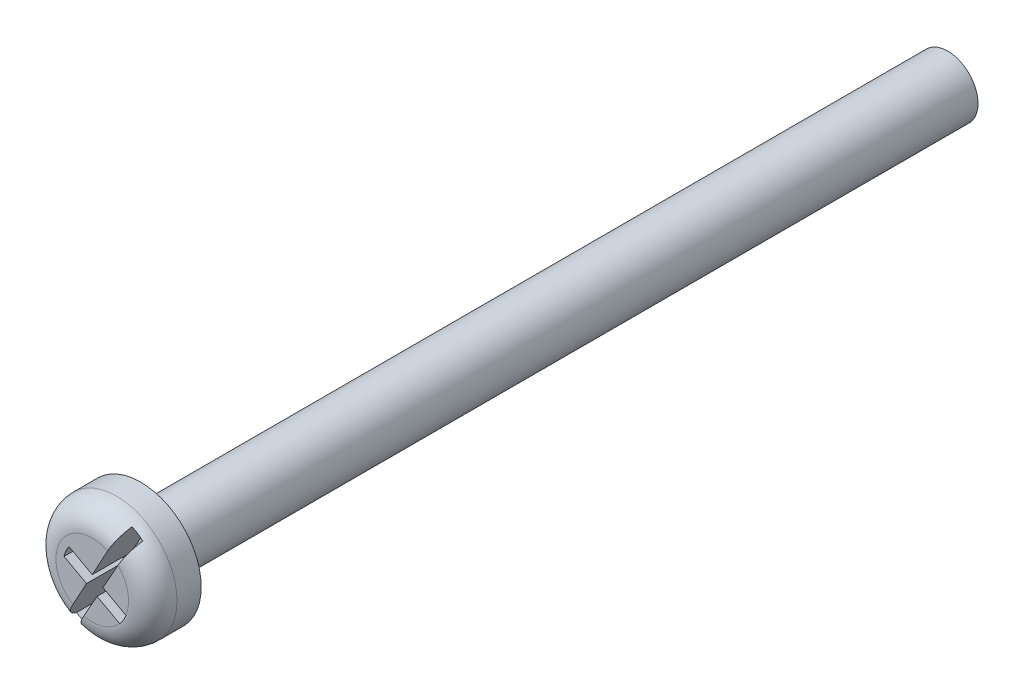
SolidWorks part; units mm, degrees
material "Stop odlewniczy stali"
ref_plane "Płaszczyzna przednia" through (0, 0, 0) normal (0, 0, 1) x (1, 0, 0)
ref_plane "Płaszczyzna górna" through (0, 0, 0) normal (0, 1, 0) x (1, 0, 0)
ref_plane "Płaszczyzna prawa" through (0, 0, 0) normal (1, 0, 0) x (0, 0, -1)
sketch "Szkic1" plane through (0, 0, 0) normal (0, 0, 1) x (1, 0, 0)
  circle A0 centre (-1.8605, 2.7321) radius 3
  dimension "D1" = 6
extrude "Dodanie-wyciągnięcie2" add sketch "Szkic1" along normal blind 2.4
sketch "Szkic2" plane through (0, 0, 0) normal (0, 0, -1) x (-1, 0, 0)
  circle A0 centre (1.8605, 2.7321) radius 1.5
extrude "Dodanie-wyciągnięcie3" add sketch "Szkic2" along normal blind 40
fillet "Zaokrąglenie2" radius 1.2 1 edges at (1.1395, 2.7321, 2.4)
sketch "Szkic3" plane through (0, 0, 2.4) normal (0, 0, 1) x (1, 0, 0)
  line L0 (-1.8595, 2.9591) -> (-0.5756, 5.3165)
  line L1 (-1.8595, 2.9591) -> (-3.0095, 3.5874)
  line L2 (-3.3345, 0.2508) -> (-2.1451, 2.4347)
  line L3 (-2.8199, 0.0102) -> (-1.6213, 2.1486)
  line L4 (-0.184, 2.0436) -> (-1.3294, 2.6694)
  line L5 (-0.4992, 1.5357) -> (-1.6213, 2.1486)
  line L6 (-1.3294, 2.6694) -> (-0.0393, 4.9711)
  line L7 (-2.1451, 2.4347) -> (-3.2587, 3.0429)
  arc A2 (-3.0095, 3.5874) -> (-3.2587, 3.0429) centre (-1.8605, 2.7321) ccw
  arc A3 (-0.0393, 4.9711) -> (-0.5756, 5.3165) centre (-1.8605, 2.7321) ccw
  arc A4 (-3.3345, 0.2508) -> (-2.8199, 0.0102) centre (-1.8605, 2.7321) ccw
  arc A6 (-0.4992, 1.5357) -> (-0.184, 2.0436) centre (-1.8605, 2.7321) ccw
extrude "Wytnij-wyciągnięcie1" cut sketch "Szkic3" against normal blind 1.94
